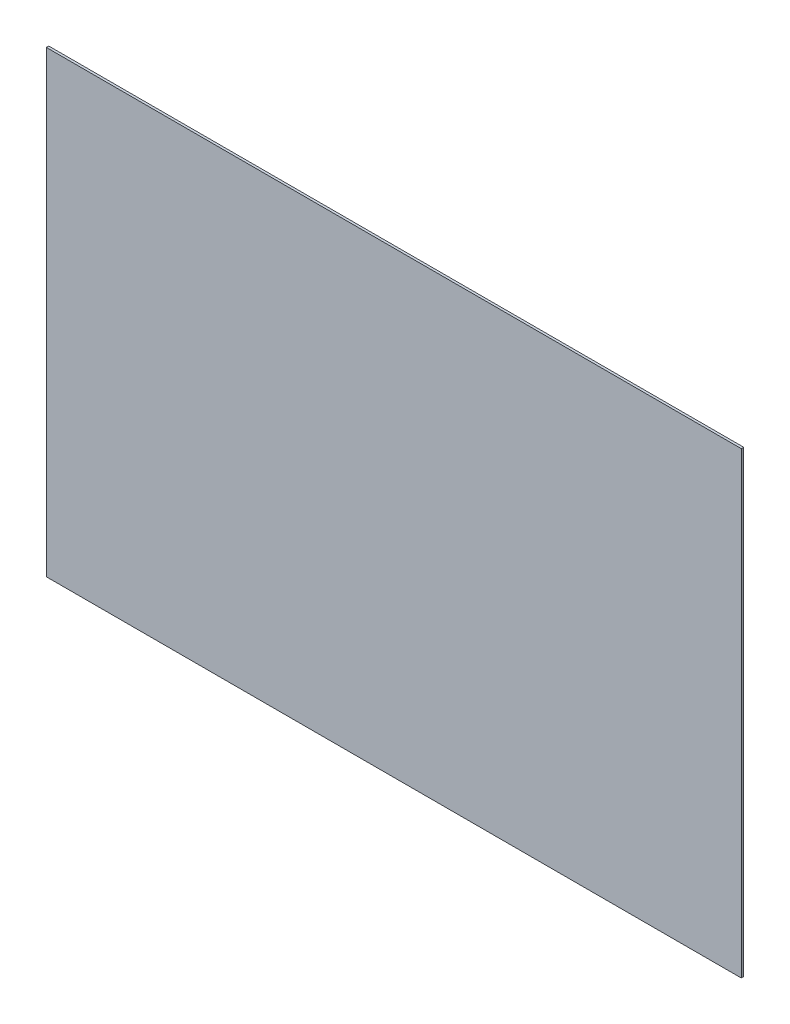
SolidWorks part; units mm, degrees
ref_plane "Front Plane" through (0, 0, 0) normal (0, 0, 1) x (1, 0, 0)
ref_plane "Top Plane" through (0, 0, 0) normal (0, 1, 0) x (1, 0, 0)
ref_plane "Right Plane" through (0, 0, 0) normal (1, 0, 0) x (0, 0, -1)
sketch "Sketch1" plane through (0, 0, 0) normal (0, 0, 1) x (1, 0, 0)
  line L1 (-457.2, 301.625) -> (457.2, 301.625)
  line L2 (-457.2, 301.625) -> (-457.2, -301.625)
  line L3 (-457.2, -301.625) -> (457.2, -301.625)
  line L4 (457.2, 301.625) -> (457.2, -301.625)
  line L5 (-457.2, 301.625) -> (457.2, -301.625) construction
  line L6 (-457.2, -301.625) -> (457.2, 301.625) construction
  point P0 (0, 0)
  dimension "D1" = 914.4
  dimension "D2" = 603.25
extrude "Boss-Extrude1" add sketch "Sketch1" along normal blind 3.175
